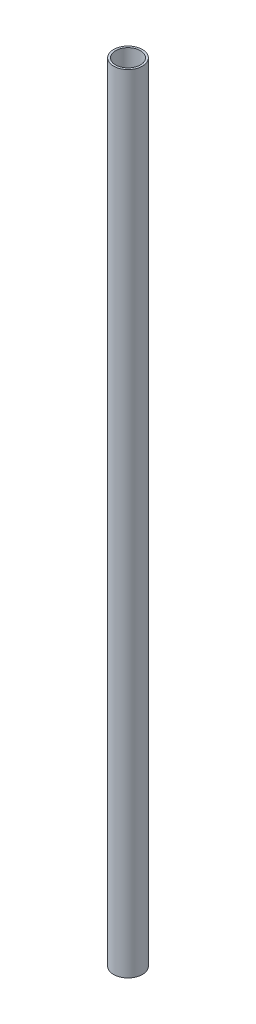
SolidWorks part; units mm, degrees
ref_plane "Front Plane" through (0, 0, 0) normal (0, 0, 1) x (1, 0, 0)
ref_plane "Top Plane" through (0, 0, 0) normal (0, 1, 0) x (1, 0, 0)
ref_plane "Right Plane" through (0, 0, 0) normal (1, 0, 0) x (0, 0, -1)
sketch "Sketch1" plane through (0, 0, 0) normal (0, 1, 0) x (1, 0, 0)
  circle A0 centre (0, 0) radius 12.7
  circle A1 centre (0, 0) radius 10.922
extrude "Boss-Extrude2" add sketch "Sketch1" along normal blind 692.15
